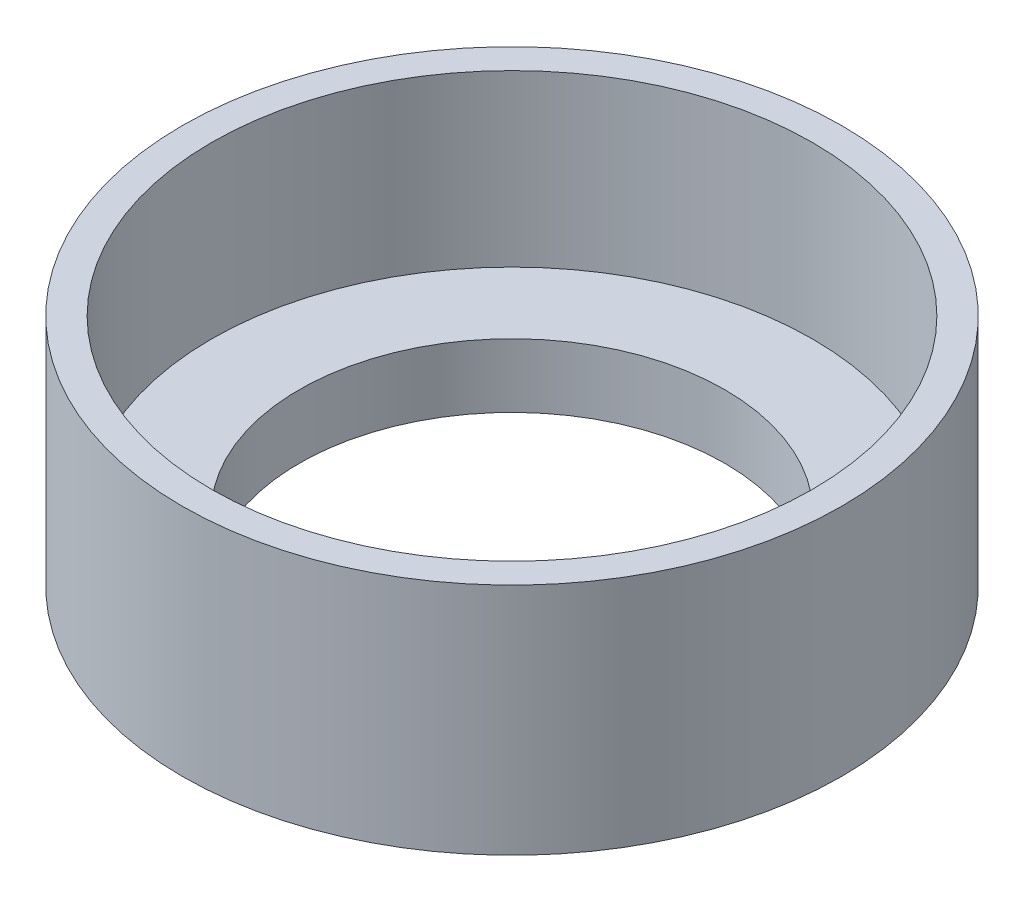
SolidWorks part; units mm, degrees
ref_plane "Front Plane" through (0, 0, 0) normal (0, 0, 1) x (1, 0, 0)
ref_plane "Top Plane" through (0, 0, 0) normal (0, 1, 0) x (1, 0, 0)
ref_plane "Right Plane" through (0, 0, 0) normal (1, 0, 0) x (0, 0, -1)
sketch "Sketch1" plane through (0, 0, 0) normal (0, 1, 0) x (1, 0, 0)
  circle A0 centre (0, 0) radius 15.5
  circle A1 centre (0, 0) radius 14.125
  dimension "D1" = 28.25
  dimension "D2" = 31
extrude "Boss-Extrude1" add sketch "Sketch1" along normal blind 8
sketch "Sketch2" plane through (0, 0, 0) normal (0, -1, 0) x (1, 0, 0)
  circle A0 centre (0, 0) radius 15.5
  circle A1 centre (0, 0) radius 10
  dimension "D1" = 20
extrude "Boss-Extrude3" add sketch "Sketch2" along normal blind 3
